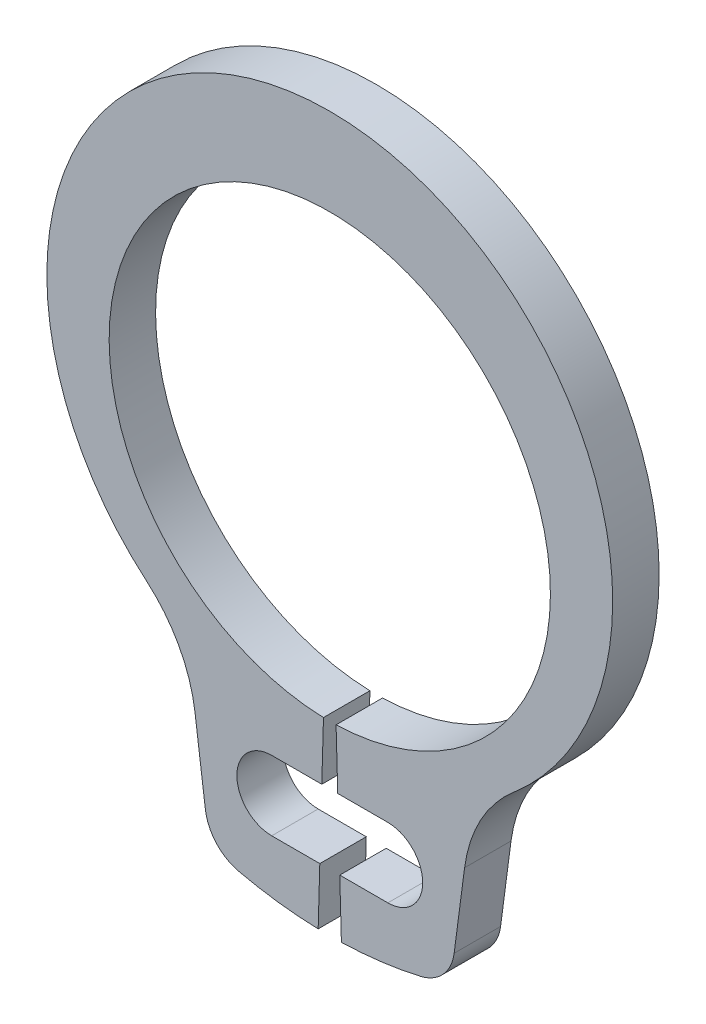
SolidWorks part; units mm, degrees
ref_plane "Plane1" through (0, 0, 0) normal (0, 0, 1) x (1, 0, 0)
ref_plane "Plane2" through (0, 0, 0) normal (0, 1, 0) x (1, 0, 0)
ref_plane "Plane3" through (0, 0, 0) normal (1, 0, 0) x (0, 0, -1)
sketch "Clipboard" plane through (0, 0, 0) normal (0, 0, 1) x (1, 0, 0)
  line L0 (0, 0) -> (1.5, 0)
  line L1 (0, 0) -> (0, 0.75)
  line L2 (0, 0) -> (0, -3.2)
  circle A0 centre (0, 0) radius 0.6
  circle A1 centre (0, 0) radius 4
  dimension "HoleDia" = 1.2
sketch "BodySke" plane through (0, 0, 0) normal (0, 0, 1) x (1, 0, 0)
  line L0 (-1.5431, 0) -> (1.5431, 0) construction
  line L1 (0, 0) -> (0, 5.3) construction
  line L2 (0.1086, -3.7984) -> (0.2, -6.9971)
  line L3 (-0.1086, -3.7984) -> (-0.2, -6.9971)
  line L4 (0, 0) -> (4.7479, -5.1437) construction
  line L5 (0, 0) -> (-4.7479, -5.1437) construction
  line L7 (2.3217, -4.8243) -> (2.142, -6.1894)
  line L8 (-2.3217, -4.8243) -> (-2.142, -6.1894)
  circle A0 centre (0, 0) radius 3.8 construction
  arc A1 (0.1086, -3.7984) -> (-0.1086, -3.7984) centre (0, 0) ccw
  arc A2 (3.0861, -3.3434) -> (-3.0861, -3.3434) centre (0, 0.4273) ccw construction
  arc A3 (0.2, -6.9971) -> (1.5662, -6.8225) centre (0, 0) ccw
  arc A4 (3.1606, -3.2812) -> (2.3217, -4.8243) centre (4.7479, -5.1437) ccw
  arc A5 (-2.3217, -4.8243) -> (-3.1606, -3.2812) centre (-4.7479, -5.1437) ccw
  arc A6 (-1.5662, -6.8225) -> (-0.2, -6.9971) centre (0, 0) ccw
  arc A7 (3.1606, -3.2812) -> (-3.1606, -3.2812) centre (0, 0.4273) ccw
  arc A8 (-2.299, -4.9964) -> (2.299, -4.9964) centre (0, 0) ccw construction
  circle A9 centre (1, -5.4083) radius 0.6
  circle A10 centre (-1, -5.4083) radius 0.6
  arc A11 (2.142, -6.1894) -> (1.5662, -6.8225) centre (1.3984, -6.0916) cw
  arc A12 (-2.142, -6.1894) -> (-1.5662, -6.8225) centre (-1.3984, -6.0916) ccw
  point P28 (2.0768, -6.6848)
  point P31 (-2.0768, -6.6848)
  dimension "HoleDia" = 1.2
  dimension "D3" = 0.75
  dimension "D2" = 15
extrude "Body" add sketch "BodySke" against normal blind 0.8
sketch "NotSke" plane through (0, 0, 0) normal (0, 0, 1) x (1, 0, 0)
  line L0 (1, -4.8083) -> (1, -6.0083)
  line L1 (1, -6.0083) -> (-1, -6.0083)
  line L2 (-1, -6.0083) -> (-1, -4.8083)
  line L3 (-1, -4.8083) -> (1, -4.8083)
  circle A0 centre (1, -5.4083) radius 0.6 construction
  circle A1 centre (-1, -5.4083) radius 0.6 construction
extrude "Notch" cut sketch "NotSke" against normal through all
sketch "UnlSke" plane through (0, 0, 0) normal (0, 0, 1) x (1, 0, 0)
  line L0 (-2.016, -6.7034) -> (-1.0944, -3.639)
  line L1 (2.016, -6.7034) -> (1.0944, -3.639)
  arc A0 (1.0944, -3.639) -> (-1.0944, -3.639) centre (0, 0) ccw
  arc A1 (2.016, -6.7034) -> (-2.016, -6.7034) centre (0, 0) ccw
  arc A2 (0.2, -6.9971) -> (1.5662, -6.8225) centre (0, 0) ccw construction
  arc A3 (0.1086, -3.7984) -> (-0.1086, -3.7984) centre (0, 0) ccw construction
  circle A4 centre (-1, -5.4083) radius 0.6 construction
  circle A5 centre (1, -5.4083) radius 0.6 construction
extrude "Unlug" [suppressed] add sketch "UnlSke" against normal through all
equation "' \"ShaftDia@Clipboard\" = 3"
equation "' \"Thickness@Body\" = 0.4"
equation "' \"GrooveDia@BodySke\" = 2.8"
equation "' \"LugSection@Clipboard\" = 1.9"
equation "' \"LargeSection@Clipboard\" = 0.8"
equation "' \"HoleDia@Clipboard\" = 1.0"
equation "' \"ShaftDia@Clipboard\" = 10"
equation "' \"Thickness@Body\" = 1.0"
equation "' \"GrooveDia@BodySke\" = 9.6"
equation "' \"LugSection@Clipboard\" = 3.3"
equation "' \"LargeSection@Clipboard\" = 1.8"
equation "' \"HoleDia@Clipboard\" = 1.5"
equation "\"SmallSection@Clipboard\" = \"LargeSection@Clipboard\" * 0.5"
equation "\"Gap@BodySke\" =  \"Thickness@Body\" / 2"
equation "\"LargeRad@BodySke\" =  \"GrooveDia@BodySke\" / 2 +  \"LargeSection@Clipboard\""
equation "\"SmallRad@BodySke\" =  \"GrooveDia@BodySke\" / 2 +  \"SmallSection@Clipboard\""
equation "\"LugRad@BodySke\" = \"GrooveDia@BodySke\" / 2 + \"LugSection@Clipboard\""
equation "\"HoleOffsetRad@BodySke\" = (  \"ShaftDia@Clipboard\" / 2 + \"LugRad@BodySke\" ) / 2"
equation "\"HoleSpacing@BodySke\" = \"Gap@BodySke\"  * 2 +  \"HoleDia@Clipboard\""
equation "\"HoleDia@BodySke\" =  \"HoleDia@Clipboard\""
equation "\"SmallAngle@BodySke\" = atn(\"HoleSpacing@BodySke\" / 2 / sqr(\"HoleOffsetRad@BodySke\"  * \"HoleOffsetRad@BodySke\" - (\"HoleSpacing@BodySke\" / 2) * (\"HoleSpacing@BodySke\" / 2) ))  * 7 *  (\"LargeRad@BodySke\" / \"SmallRad@BodySke\")* ( 180 / 3.141593)"
